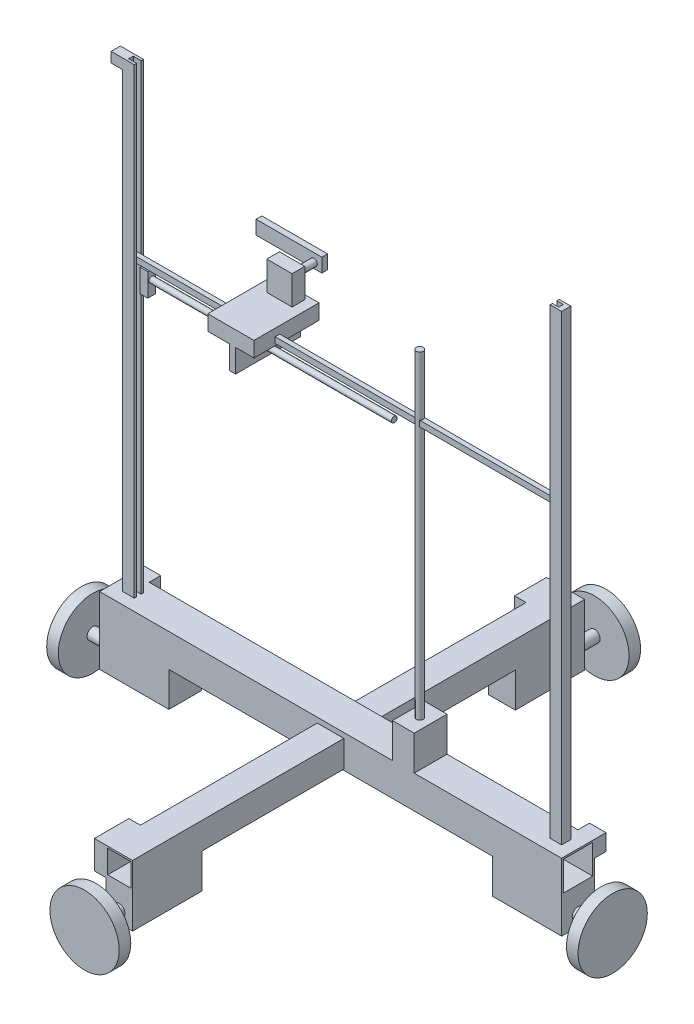
SolidWorks part; units mm, degrees
ref_plane "Front Plane" through (0, 0, 0) normal (0, 0, 1) x (1, 0, 0)
ref_plane "Top Plane" through (0, 0, 0) normal (0, 1, 0) x (1, 0, 0)
ref_plane "Right Plane" through (0, 0, 0) normal (1, 0, 0) x (0, 0, -1)
sketch "Sketch1" plane through (0, 0, 0) normal (1, 0, 0) x (0, 0, -1)
  line L1 (12.7, -12.7) -> (-12.7, -12.7)
  line L2 (12.7, -12.7) -> (12.7, 12.7)
  line L3 (12.7, 12.7) -> (-12.7, 12.7)
  line L4 (-12.7, -12.7) -> (-12.7, 12.7)
  line L5 (12.7, -12.7) -> (-12.7, 12.7) construction
  line L6 (12.7, 12.7) -> (-12.7, -12.7) construction
  point P0 (0, 0)
  dimension "D1" = 25.4
  dimension "D2" = 25.4
extrude "Extrude-Thin1" add sketch "Sketch1" along normal blind 400 thin contours L3 L4 L1 L2 thin type one direction wall 1.5
sketch "Sketch2" plane through (0, 0, 14.2) normal (0, 0, 1) x (1, 0, 0)
  line L0 (0, -14.2) -> (0, 14.2) construction
  line L1 (210, -11.6936) -> (190, -11.6936)
  line L2 (210, -11.6936) -> (210, 8.3064)
  line L3 (210, 8.3064) -> (190, 8.3064)
  line L4 (190, -11.6936) -> (190, 8.3064)
  line L5 (210, -11.6936) -> (190, 8.3064) construction
  line L6 (210, 8.3064) -> (190, -11.6936) construction
  point P0 (200, -1.6936)
  dimension "D1" = 20
  dimension "D2" = 20
  dimension "D3" = 200
extrude "Extrude-Thin2" add sketch "Sketch2" along normal blind 183 and the other way blind 208.4 thin thin type one direction wall 1.5
sketch "Sketch3" plane through (0, -14.2, 0) normal (0, -1, 0) x (-1, 0, 0)
  line L0 (-400, 14.2) -> (0, 14.2) construction
  line L1 (-400, -14.2) -> (-340, -14.2)
  line L2 (-400, -14.2) -> (-400, 14.2)
  line L3 (-400, 14.2) -> (-340, 14.2)
  line L4 (-340, -14.2) -> (-340, 14.2)
  line L6 (0, -14.2) -> (-60, -14.2)
  line L7 (0, -14.2) -> (0, 14.2)
  line L8 (0, 14.2) -> (-60, 14.2)
  line L9 (-60, -14.2) -> (-60, 14.2)
  dimension "D1" = 60
  dimension "D2" = 28.4
  dimension "D3" = 60
extrude "Boss-Extrude1" add sketch "Sketch3" along normal blind 30
sketch "Sketch4" plane through (0, -13.1936, 0) normal (0, -1, 0) x (-1, 0, 0)
  line L0 (-188.5, -14.2) -> (-188.5, -197.2) construction
  line L1 (-211.5, -197.2) -> (-188.5, -197.2)
  line L2 (-211.5, -197.2) -> (-211.5, -137.2)
  line L3 (-211.5, -137.2) -> (-188.5, -137.2)
  line L4 (-188.5, -197.2) -> (-188.5, -137.2)
  line L5 (-188.5, 194.2) -> (-188.5, 14.2) construction
  line L6 (-211.5, 194.2) -> (-188.5, 194.2)
  line L7 (-211.5, 194.2) -> (-211.5, 134.2)
  line L8 (-211.5, 134.2) -> (-188.5, 134.2)
  line L9 (-188.5, 194.2) -> (-188.5, 134.2)
  dimension "D1" = 60
extrude "Boss-Extrude2" add sketch "Sketch4" along normal blind 30
sketch "Sketch5" plane through (400, 0, 0) normal (1, 0, 0) x (0, 0, -1)
  line L0 (14.2, -44.2) -> (-14.2, -44.2) construction
  circle A0 centre (0, -34.2) radius 5
  dimension "D1" = 10
extrude "Boss-Extrude3" add sketch "Sketch5" along normal blind 30
sketch "Sketch6" plane through (0, 0, -194.2) normal (0, 0, -1) x (-1, 0, 0)
  line L0 (-188.5, -43.1936) -> (-211.5, -43.1936) construction
  circle A0 centre (-200, -33.1936) radius 5
  dimension "D1" = 10
extrude "Boss-Extrude4" add sketch "Sketch6" along normal blind 30
sketch "Sketch7" plane through (0, 0, 0) normal (-1, 0, 0) x (0, 0, 1)
  line L0 (14.2, -44.2) -> (-14.2, -44.2) construction
  circle A0 centre (0, -34.2) radius 5
  dimension "D1" = 10
extrude "Boss-Extrude5" add sketch "Sketch7" along normal blind 30
sketch "Sketch8" plane through (0, 0, 197.2) normal (0, 0, 1) x (1, 0, 0)
  line L0 (211.5, -43.1936) -> (188.5, -43.1936) construction
  circle A0 centre (200, -33.1936) radius 5
  dimension "D1" = 10
extrude "Boss-Extrude6" add sketch "Sketch8" along normal blind 30
sketch "Sketch9" plane through (0, 14.2, 0) normal (0, 1, 0) x (1, 0, 0)
  line L0 (10, 3.8) -> (20, 3.8)
  line L1 (20, -2.2) -> (20, -4.2)
  line L2 (10, 3.8) -> (10, -4.2)
  line L3 (10, -4.2) -> (20, -4.2)
  line L4 (20, 3.8) -> (20, 1.8)
  line L5 (0, 14.2) -> (0, -14.2) construction
  line L6 (20, 1.8) -> (13.1775, 1.8)
  line L7 (400, 14.2) -> (400, -14.2) construction
  line L8 (20, -2.2) -> (13.1775, -2.2)
  line L9 (13.1775, 1.8) -> (13.1775, -2.2)
  line L10 (380, 3.8) -> (390, 3.8)
  line L11 (380, 3.8) -> (380, 1.8)
  line L12 (380, -4.2) -> (390, -4.2)
  line L13 (390, 3.8) -> (390, -4.2)
  line L14 (400, -14.2) -> (0, -14.2) construction
  line L15 (380, -2.2) -> (380, -4.2)
  line L16 (380, 1.8) -> (385.5268, 1.8)
  line L18 (380, -2.2) -> (385.5268, -2.2)
  line L19 (385.5268, 1.8) -> (385.5268, -2.2)
  dimension "D1" = 10
  dimension "D2" = 10
  dimension "D3" = 4
  dimension "D4" = 2
  dimension "D5" = 10
  dimension "D6" = 10
  dimension "D7" = 8
  dimension "D8" = 10
  dimension "D9" = 2
  dimension "D10" = 10
  dimension "D11" = 4
  dimension "D12" = 2
extrude "Boss-Extrude7" add sketch "Sketch9" along normal blind 400
ref_plane "Plane1" through (0, 264.2, 0) normal (0, 1, 0) x (1, 0, 0)
sketch "Sketch10" plane through (0, 264.2, 0) normal (0, 1, 0) x (1, 0, 0)
  line L0 (385.5268, 1.8) -> (385.5268, -2.2) construction
  line L1 (13.1775, -2.2) -> (385.5268, -2.2)
  line L2 (13.1775, -2.2) -> (13.1775, 1.8)
  line L3 (13.1775, 1.8) -> (385.5268, 1.8)
  line L4 (385.5268, -2.2) -> (385.5268, 1.8)
  line L5 (385.5268, 1.8) -> (385.5268, -2.2) construction
extrude "Boss-Extrude8" add sketch "Sketch10" along normal blind 5
sketch "Sketch24" plane through (0, 0, -224.2) normal (0, 0, -1) x (-1, 0, 0)
  circle A0 centre (-200, -33.1936) radius 30
extrude "Boss-Extrude20" add sketch "Sketch24" against normal blind 10
sketch "Sketch25" plane through (-30, 0, 0) normal (-1, 0, 0) x (0, 0, 1)
  circle A0 centre (0, -34.2) radius 30
extrude "Boss-Extrude21" add sketch "Sketch25" against normal blind 10
sketch "Sketch26" plane through (0, 0, 227.2) normal (0, 0, 1) x (1, 0, 0)
  circle A0 centre (200, -33.1936) radius 30
extrude "Boss-Extrude22" add sketch "Sketch26" against normal blind 10
sketch "Sketch27" plane through (430, 0, 0) normal (1, 0, 0) x (0, 0, -1)
  circle A0 centre (0, -34.2) radius 30
extrude "Boss-Extrude23" add sketch "Sketch27" against normal blind 10
sketch "Sketch28" plane through (0, 14.2, 0) normal (0, 1, 0) x (1, 0, 0)
  line L0 (400, 14.2) -> (0, 14.2) construction
  line L1 (253.5348, 14.2) -> (272.3941, 14.2)
  line L2 (253.5348, 14.2) -> (253.5348, -14.2)
  line L3 (253.5348, -14.2) -> (272.3941, -14.2)
  line L4 (272.3941, 14.2) -> (272.3941, -14.2)
  line L5 (400, -14.2) -> (0, -14.2) construction
extrude "Boss-Extrude24" add sketch "Sketch28" along normal blind 30
sketch "Sketch29" plane through (0, 44.2, 0) normal (0, 1, 0) x (1, 0, 0)
  circle A0 centre (262.9782, 0) radius 3
extrude "Boss-Extrude25" add sketch "Sketch29" along normal blind 276
ref_plane "Plane2" through (100, 0, 0) normal (1, 0, 0) x (0, 0, -1)
sketch "Sketch30" plane through (100, 0, 0) normal (1, 0, 0) x (0, 0, -1)
  line L1 (-20.5449, 262.4523) -> (35.7355, 262.4523)
  line L2 (-20.5449, 262.4523) -> (-20.5449, 275.6502)
  line L3 (-20.5449, 275.6502) -> (35.7355, 275.6502)
  line L4 (35.7355, 262.4523) -> (35.7355, 275.6502)
extrude "Boss-Extrude26" add sketch "Sketch30" along normal blind 40 contours L3 L4 L1 L2
sketch "Sketch31" plane through (0, 264.2, 0) normal (0, -1, 0) x (-1, 0, 0)
  line L1 (-24.196, -3.4692) -> (-30.992, -3.4692)
  line L2 (-24.196, -3.4692) -> (-24.196, 3.3145)
  line L3 (-24.196, 3.3145) -> (-30.992, 3.3145)
  line L4 (-30.992, -3.4692) -> (-30.992, 3.3145)
extrude "Boss-Extrude27" add sketch "Sketch31" along normal blind 20
sketch "Sketch32" plane through (30.992, 0, 0) normal (1, 0, 0) x (0, 0, -1)
  circle A0 centre (0, 256.5641) radius 2.5
extrude "Boss-Extrude28" add sketch "Sketch32" along normal blind 210
sketch "Sketch33" plane through (0, 262.4523, 0) normal (0, -1, 0) x (-1, 0, 0)
  line L0 (-140, -20.5449) -> (-100, -20.5449) construction
  line L1 (-124.1341, -20.5449) -> (-118.9458, -20.5449)
  line L2 (-124.1341, -20.5449) -> (-124.1341, 35.7355)
  line L3 (-124.1341, 35.7355) -> (-118.9458, 35.7355)
  line L4 (-118.9458, -20.5449) -> (-118.9458, 35.7355)
  line L5 (-140, 35.7355) -> (-100, 35.7355) construction
extrude "Boss-Extrude29" add sketch "Sketch33" along normal blind 20
sketch "Sketch34" plane through (0, 275.6502, 0) normal (0, 1, 0) x (1, 0, 0)
  line L1 (109.5688, 31.937) -> (131.4935, 31.937)
  line L2 (109.5688, 31.937) -> (109.5688, 20.9696)
  line L3 (109.5688, 20.9696) -> (131.4935, 20.9696)
  line L4 (131.4935, 31.937) -> (131.4935, 20.9696)
extrude "Boss-Extrude30" add sketch "Sketch34" along normal blind 25
sketch "Sketch35" plane through (0, 0, -31.937) normal (0, 0, -1) x (-1, 0, 0)
  circle A0 centre (-119.3784, 287.6807) radius 3
extrude "Boss-Extrude31" add sketch "Sketch35" along normal blind 20
sketch "Sketch36" plane through (0, 0, -51.937) normal (0, 0, -1) x (-1, 0, 0)
  line L1 (-126.2666, 294.9177) -> (-69.3784, 294.9177)
  line L2 (-126.2666, 294.9177) -> (-126.2666, 283.0055)
  line L3 (-126.2666, 283.0055) -> (-69.3784, 283.0055)
  line L4 (-69.3784, 294.9177) -> (-69.3784, 283.0055)
  circle A0 centre (-119.3784, 287.6807) radius 3 construction
  dimension "D1" = 50
extrude "Boss-Extrude32" add sketch "Sketch36" along normal blind 5
sketch "Sketch37" plane through (10, 0, 0) normal (-1, 0, 0) x (0, 0, 1)
  line L0 (-3.8, 414.2) -> (-3.8, 14.2) construction
  line L1 (4.2, 414.2) -> (-3.8, 414.2)
  line L2 (4.2, 414.2) -> (4.2, 405.4245)
  line L3 (4.2, 405.4245) -> (-3.8, 405.4245)
  line L4 (-3.8, 414.2) -> (-3.8, 405.4245)
extrude "Boss-Extrude33" add sketch "Sketch37" along normal blind 10
sketch "Sketch38" plane through (188.5, 0, 0) normal (-1, 0, 0) x (0, 0, 1)
  line L1 (-194.2, 9.8064) -> (-166.5935, 9.8064)
  line L2 (-194.2, 9.8064) -> (-194.2, -14.5631)
  line L3 (-194.2, -14.5631) -> (-166.5935, -14.5631)
  line L4 (-166.5935, 9.8064) -> (-166.5935, -14.5631)
  line L5 (197.2, 9.8064) -> (167.3383, 9.8064)
  line L6 (197.2, 9.8064) -> (197.2, -14.5631)
  line L7 (197.2, -14.5631) -> (167.3383, -14.5631)
  line L8 (167.3383, 9.8064) -> (167.3383, -14.5631)
extrude "Boss-Extrude34" add sketch "Sketch38" along normal blind 10
sketch "Sketch39" plane through (0, 0, -14.2) normal (0, 0, -1) x (-1, 0, 0)
  line L1 (0, 14.2) -> (-14.5369, 14.2)
  line L2 (0, 14.2) -> (0, -4.2097)
  line L3 (0, -4.2097) -> (-14.5369, -4.2097)
  line L4 (-14.5369, 14.2) -> (-14.5369, -4.2097)
  line L5 (-400, 14.2) -> (-385.7356, 14.2)
  line L6 (-400, 14.2) -> (-400, 0)
  line L7 (-400, 0) -> (-385.7356, 0)
  line L8 (-385.7356, 14.2) -> (-385.7356, 0)
extrude "Boss-Extrude35" add sketch "Sketch39" along normal blind 10
